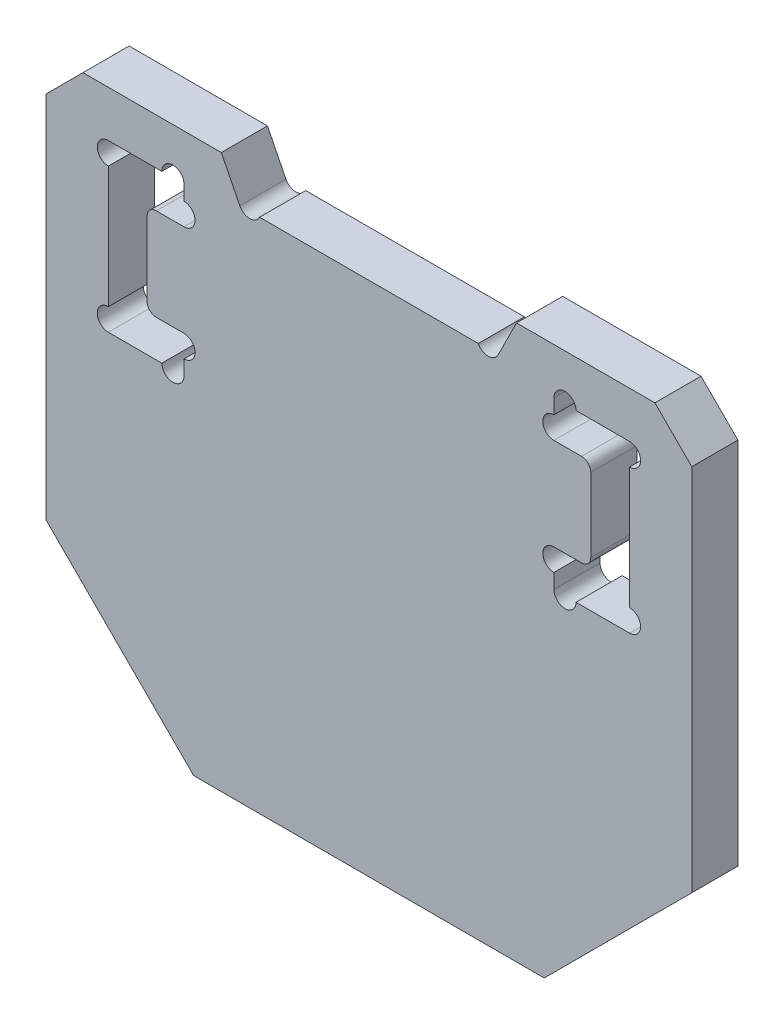
SolidWorks part; units mm, degrees
ref_plane "前视基准面" through (0, 0, 0) normal (0, 0, 1) x (1, 0, 0)
ref_plane "上视基准面" through (0, 0, 0) normal (0, 1, 0) x (1, 0, 0)
ref_plane "右视基准面" through (0, 0, 0) normal (1, 0, 0) x (0, 0, -1)
sketch "草图1" plane through (0, 0, 0) normal (0, 0, 1) x (1, 0, 0)
  line L0 (17.5, 0) -> (-17.5, 0)
  line L1 (-17.5, 0) -> (-17.5, -30)
  line L2 (-17.5, -30) -> (17.5, -30)
  line L3 (17.5, -30) -> (17.5, 0)
  point P4 (0, 0)
  dimension "D1" = 35
  dimension "D2" = 30
extrude "凸台-拉伸1" add sketch "草图1" along normal mid plane 2.5
chamfer "倒角1" distance 8 angle 45 2 edges at (17.5, -30, 0) (-17.5, -30, 0)
chamfer "倒角2" distance 2 angle 45 2 edges at (17.5, 0, 0) (-17.5, 0, 0)
sketch "草图2" plane through (0, 0, 1.25) normal (0, 0, 1) x (1, 0, 0)
  line L0 (-8, 0) -> (-7, -2)
  line L1 (15.5, 0) -> (-15.5, 0) construction
  line L2 (-7, -2) -> (7, -2)
  line L3 (7, -2) -> (8, 0)
  line L4 (8, 0) -> (-8, 0)
  line L8 (-17.5, -2) -> (-17.5, -22) construction
  point P6 (7.5306, -2.3018)
  point P8 (9.8903, 0)
  point P9 (11.0579, 0)
  point P10 (0, 0)
  dimension "D1" = 2
  dimension "D2" = 16
  dimension "D3" = 14
  dimension "D4" = 17.5
extrude "切除-拉伸1" cut sketch "草图2" against normal through all
sketch "草图4" plane through (0, 0, 1.25) normal (0, 0, 1) x (1, 0, 0)
  line L0 (-14.125, -2.5) -> (-10.025, -2.5)
  line L1 (-10.025, -2.5) -> (-10.025, -4.5)
  line L2 (-10.025, -4.5) -> (-12.025, -4.5)
  line L3 (-12.025, -4.5) -> (-12.025, -9.5)
  line L4 (-12.025, -9.5) -> (-10.025, -9.5)
  line L5 (-10.025, -9.5) -> (-10.025, -11.5)
  line L6 (-10.025, -11.5) -> (-14.125, -11.5)
  line L7 (-14.125, -11.5) -> (-14.125, -2.5)
  line L8 (0, -2.5) -> (0, -11.5) construction
  line L10 (-17.5, -2) -> (-17.5, -22) construction
  line L11 (10.025, -11.5) -> (14.125, -11.5)
  line L12 (10.025, -9.5) -> (10.025, -11.5)
  line L13 (12.025, -9.5) -> (10.025, -9.5)
  line L14 (12.025, -4.5) -> (12.025, -9.5)
  line L15 (10.025, -4.5) -> (12.025, -4.5)
  line L16 (10.025, -2.5) -> (10.025, -4.5)
  line L17 (14.125, -2.5) -> (10.025, -2.5)
  line L18 (14.125, -11.5) -> (14.125, -2.5)
  line L19 (15.5, 0) -> (8, 0) construction
  point P12 (0, -2)
  point P13 (0, -3.4574)
  point P24 (0, -14.3771)
  dimension "D1" = 5
  dimension "D2" = 9
  dimension "D3" = 20.05
  dimension "D4" = 2
  dimension "D5" = 2.1
  dimension "D6" = 2.5
  dimension "D7" = 17.5
extrude "切除-拉伸2" cut sketch "草图4" against normal through all
sketch "草图5" plane through (0, 0, 1.25) normal (0, 0, 1) x (1, 0, 0)
  line L0 (-14.125, -2.5) -> (-14.125, -11.5) construction
  line L1 (-14.125, -11.5) -> (-10.025, -11.5) construction
  line L2 (-10.025, -11.5) -> (-10.025, -9.5) construction
  line L4 (-10.025, -2.5) -> (-14.125, -2.5) construction
  line L5 (14.125, -2.5) -> (10.025, -2.5) construction
  line L6 (10.025, -2.5) -> (10.025, -4.5) construction
  line L7 (10.025, -9.5) -> (10.025, -11.5) construction
  line L8 (10.025, -11.5) -> (14.125, -11.5) construction
  line L9 (14.125, -11.5) -> (14.125, -2.5) construction
  line L10 (-10.025, -4.5) -> (-10.025, -2.5) construction
  line L12 (-8, 0) -> (-7, -2) construction
  line L13 (7, -2) -> (8, 0) construction
  circle A0 centre (-14.125, -3.1) radius 0.6
  circle A1 centre (-14.125, -10.9) radius 0.6
  circle A2 centre (-10.625, -11.5) radius 0.6
  circle A3 centre (-10.025, -10.1) radius 0.6
  circle A4 centre (-10.025, -3.9) radius 0.6
  circle A5 centre (-10.625, -2.5) radius 0.6
  circle A6 centre (10.625, -2.5) radius 0.6
  circle A7 centre (10.025, -3.9) radius 0.6
  circle A8 centre (10.025, -10.1) radius 0.6
  circle A9 centre (10.625, -11.5) radius 0.6
  circle A10 centre (14.125, -10.9) radius 0.6
  circle A11 centre (14.125, -3.1) radius 0.6
  circle A12 centre (-6.4633, -1.7317) radius 0.6
  circle A13 centre (6.4633, -1.7317) radius 0.6
  dimension "D1" = 1.2
extrude "切除-拉伸3" cut sketch "草图5" against normal through all
fillet "圆角1" radius 0.5 4 edges at (12.025, -9.5, 0) (12.025, -4.5, 0) (-12.025, -9.5, 0) (-12.025, -4.5, 0)
